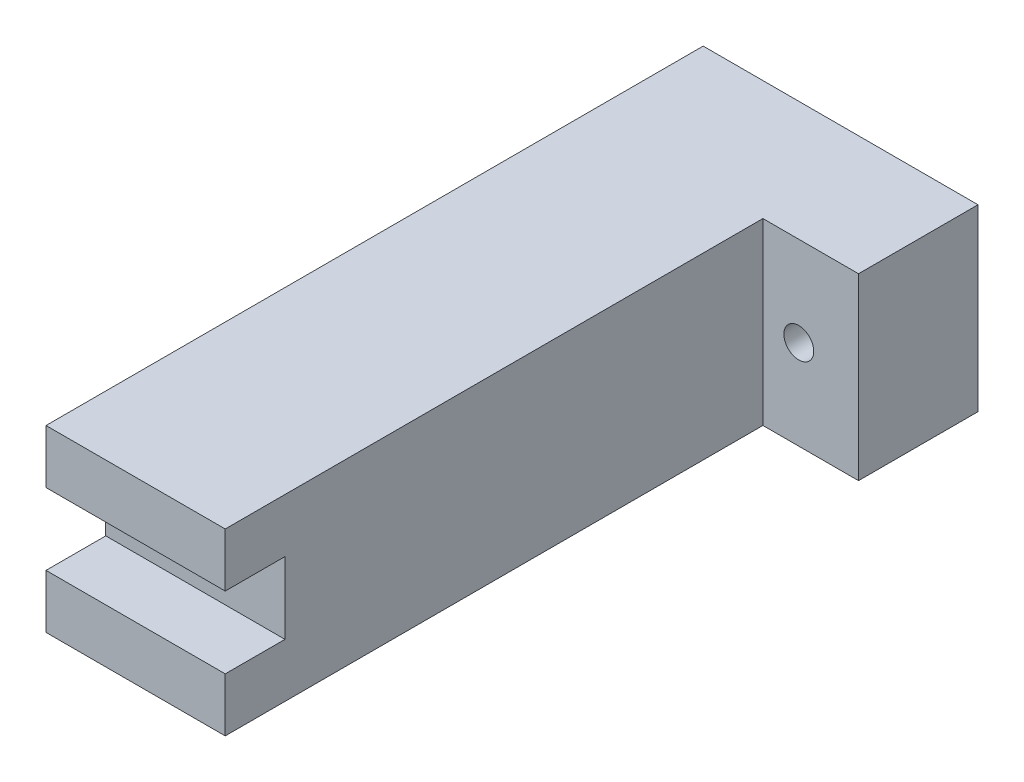
SolidWorks part; units mm, degrees
material "ПВХ Жесткий"
ref_plane "Спереди" through (0, 0, 0) normal (0, 0, 1) x (1, 0, 0)
ref_plane "Сверху" through (0, 0, 0) normal (0, 1, 0) x (1, 0, 0)
ref_plane "Справа" through (0, 0, 0) normal (1, 0, 0) x (0, 0, -1)
sketch "Эскиз1" plane through (0, 0, 0) normal (0, 1, 0) x (1, 0, 0)
  line L0 (0, 0) -> (0, -90)
  line L1 (0, -90) -> (-30, -90)
  line L2 (-30, -90) -> (-30, 20)
  line L3 (-30, 20) -> (16, 20)
  line L4 (16, 20) -> (16, 0)
  line L5 (16, 0) -> (0, 0)
  dimension "D1" = 20
  dimension "D2" = 16
  dimension "D3" = 46
  dimension "D4" = 110
extrude "Бобышка-Вытянуть1" add sketch "Эскиз1" along normal blind 30
sketch "Эскиз2" plane through (0, 0, 0) normal (0, 0, 1) x (1, 0, 0)
  line L0 (0, 30) -> (16, 30) construction
  line L1 (0, 30) -> (0, 0) construction
  circle A0 centre (6, 15) radius 2.5
  dimension "D1" = 5
  dimension "D2" = 15
  dimension "D3" = 6
extrude "Вырез-Вытянуть1" cut sketch "Эскиз2" against normal through all
sketch "Эскиз3" plane through (-30, 0, 0) normal (-1, 0, 0) x (0, 0, 1)
  line L0 (90, 21) -> (80, 21)
  line L1 (90, 30) -> (90, 0) construction
  line L2 (80, 21) -> (80, 9)
  line L3 (80, 9) -> (90, 9)
  line L4 (0, 30) -> (0, 0) construction
  line L5 (90, 30) -> (0, 30) construction
  dimension "D1" = 80
  dimension "D2" = 12
  dimension "D3" = 9
extrude "Вырез-Вытянуть2" cut sketch "Эскиз3" against normal through all and the other way through all
